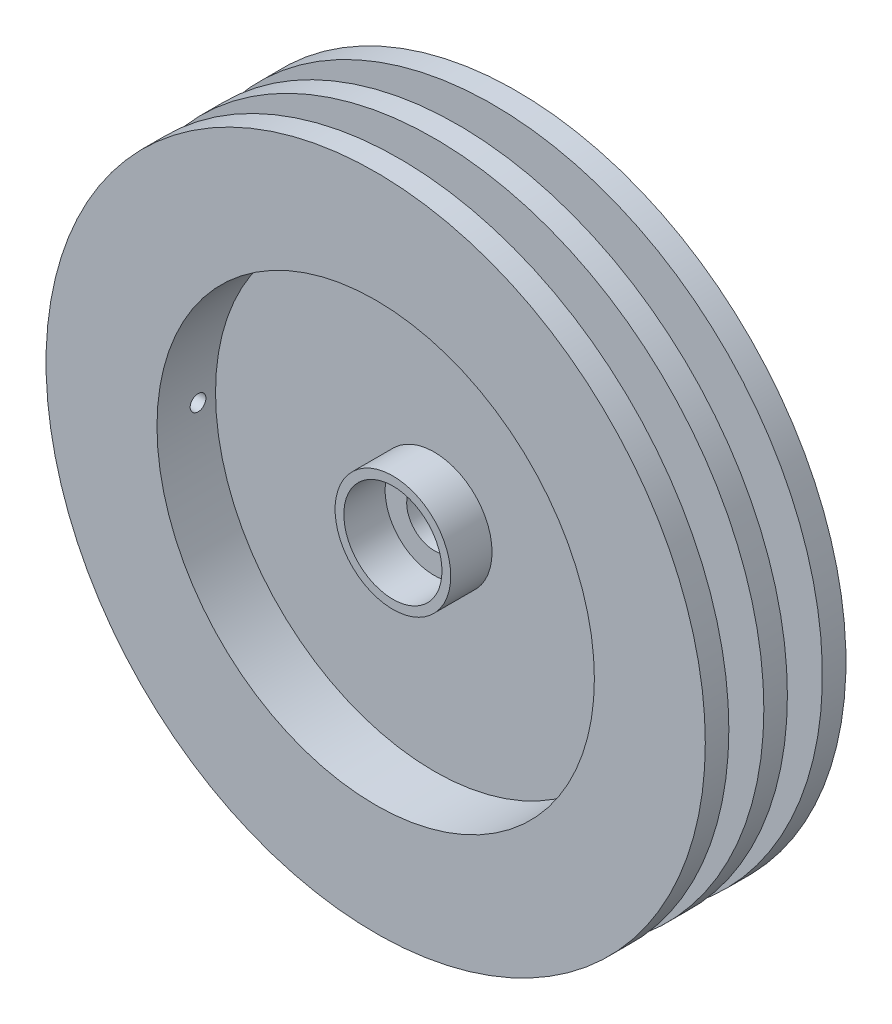
SolidWorks part; units mm, degrees
ref_plane "Front Plane" through (0, 0, 0) normal (0, 0, 1) x (1, 0, 0)
ref_plane "Top Plane" through (0, 0, 0) normal (0, 1, 0) x (1, 0, 0)
ref_plane "Right Plane" through (0, 0, 0) normal (1, 0, 0) x (0, 0, -1)
sketch "Sketch1" plane through (0, 0, 0) normal (0, 0, 1) x (1, 0, 0)
  circle A0 centre (0, 0) radius 23.9268
  dimension "D1" = 47.8536
extrude "Boss-Extrude1" add sketch "Sketch1" along normal blind 1.7094 contours A0
sketch "Sketch2" plane through (0, 0, 1.7094) normal (0, 0, 1) x (1, 0, 0)
  circle A0 centre (0, 0) radius 19.0119
  dimension "D1" = 38.0238
extrude "Boss-Extrude2" add sketch "Sketch2" along normal blind 2.54
sketch "Sketch3" plane through (0, 0, 0) normal (0, 0, -1) x (-1, 0, 0)
  circle A0 centre (0, 0) radius 19.0119
  dimension "D1" = 38.0238
extrude "Boss-Extrude3" add sketch "Sketch3" along normal blind 2.54
sketch "Sketch4" plane through (0, 0, 4.2494) normal (0, 0, 1) x (1, 0, 0)
  circle A0 centre (0, 0) radius 23.9268
  dimension "D1" = 47.8536
sketch "Sketch5" plane through (0, 0, -2.54) normal (0, 0, -1) x (-1, 0, 0)
  circle A0 centre (0, 0) radius 23.9268
  dimension "D1" = 47.8536
extrude "Boss-Extrude4" add sketch "Sketch4" along normal blind 1.7094
extrude "Boss-Extrude5" add sketch "Sketch5" along normal blind 1.7094
sketch "Sketch6" plane through (0, 0, 5.9588) normal (0, 0, 1) x (1, 0, 0)
  circle A0 centre (0, 0) radius 15.875
  dimension "D1" = 31.75
extrude "Cut-Extrude1" cut sketch "Sketch6" against normal blind 4.2494 contours A0
sketch "Sketch7" plane through (0, 0, -4.2494) normal (0, 0, -1) x (-1, 0, 0)
  circle A0 centre (0, 0) radius 15.875
  dimension "D1" = 31.75
extrude "Cut-Extrude2" cut sketch "Sketch7" against normal blind 4.2494
sketch "Sketch8" plane through (0, 0, 0) normal (1, 0, 0) x (0, 0, -1)
  line L0 (-1.7094, 0) -> (-4.2494, 0) construction
  line L1 (-1.7094, 19.0119) -> (-1.7094, -19.0119) construction
  line L2 (-4.2494, -23.9268) -> (-4.2494, 23.9268) construction
  line L3 (0, 0) -> (2.54, 0) construction
  line L4 (-0.8547, 0) -> (-0.8547, 0.9309) construction
  circle A0 centre (-2.9794, 0) radius 0.5715
  circle A1 centre (1.27, 0) radius 0.5715
  dimension "D1" = 1.143
extrude "Cut-Extrude3" cut sketch "Sketch8" against normal through all both and the other way through all
sketch "Sketch9" plane through (0, 0, 1.7094) normal (0, 0, 1) x (1, 0, 0)
  line L0 (0, -2) -> (0, 1.5) construction
  line L1 (-1.3229, 1.5) -> (1.3229, 1.5)
  arc A0 (-1.3229, 1.5) -> (1.3229, 1.5) centre (0, 0) ccw
  point P8 (0, 1.5)
  point P9 (0, 1.5)
  dimension "D1" = 4
  dimension "D2" = 3.5
extrude "Cut-Extrude4" cut sketch "Sketch9" against normal through all
sketch "Sketch10" plane through (0, 0, 1.7094) normal (0, 0, 1) x (1, 0, 0)
  circle A0 centre (0, 0) radius 3.5625
  circle A1 centre (0, 0) radius 4.1975
  dimension "D1" = 0.635
  dimension "D2" = 7.125
extrude "Boss-Extrude7" add sketch "Sketch10" along normal blind 3
sketch "Sketch11" plane through (0, 0, 0) normal (0, 0, -1) x (-1, 0, 0)
  circle A0 centre (0, 0) radius 3.5625
  circle A1 centre (0, 0) radius 4.1975
  dimension "D2" = 7.125
  dimension "D1" = 0.635
extrude "Boss-Extrude8" add sketch "Sketch11" along normal blind 3
